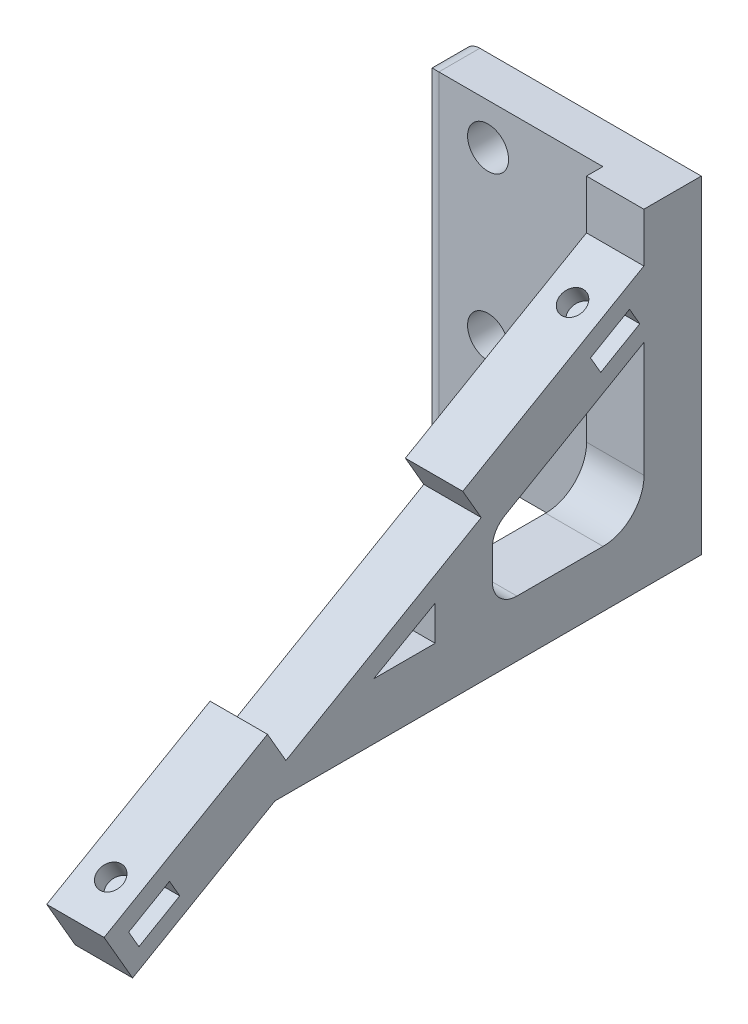
SolidWorks part; units mm, degrees
ref_plane "Front Plane" through (0, 0, 0) normal (0, 0, 1) x (1, 0, 0)
ref_plane "Top Plane" through (0, 0, 0) normal (0, 1, 0) x (1, 0, 0)
ref_plane "Right Plane" through (0, 0, 0) normal (1, 0, 0) x (0, 0, -1)
other "Mesh1"
sketch "Sketch1" plane through (0, 0, 0) normal (1, 0, 0) x (0, 0, -1)
  line L0 (-90932.5796, -4234.1019) -> (-71013.9953, 7265.8981)
  line L1 (-71013.9953, 7265.8981) -> (-68763.9953, 3368.7838)
  line L2 (-68763.9953, 3368.7838) -> (-44948.2967, 17118.7838)
  line L3 (-44948.2967, 17118.7838) -> (-47198.2967, 21015.8981)
  line L4 (-47198.2967, 21015.8981) -> (-25114.6489, 33765.8981)
  line L5 (-25114.6489, 33765.8981) -> (-25114.6489, 39765.8981)
  line L6 (-25114.6489, 39765.8981) -> (-18114.6489, 39765.8981)
  line L7 (-18114.6489, 39765.8981) -> (-18114.6489, -234.1019)
  line L8 (-90932.5796, -4234.1019) -> (-89130.3388, -4234.1019) construction
  line L9 (-18114.6489, -234.1019) -> (-70107.2704, -234.1019)
  line L10 (-70107.2704, -234.1019) -> (-87458.3031, -10251.7253)
  line L11 (-90932.5796, -4234.1019) -> (-87458.3031, -10251.7253)
  line L12 (-87940.7843, -5162.9479) -> (-82961.1382, -2287.9479)
  line L13 (-82961.1382, -2287.9479) -> (-81711.1382, -4453.0115)
  line L14 (-81711.1382, -4453.0115) -> (-86690.7843, -7328.0115)
  line L15 (-86690.7843, -7328.0115) -> (-87940.7843, -5162.9479)
  line L16 (-58064.4113, 6650.0317) -> (-50564.4113, 10900.0317)
  line L17 (-50564.4113, 10900.0317) -> (-50564.4113, 6650.0317)
  line L18 (-50564.4113, 6650.0317) -> (-58064.4113, 6650.0317)
  line L19 (-31627.1311, 27323.1447) -> (-26867.0679, 30078.4664)
  line L20 (-26867.0679, 30078.4664) -> (-25614.6489, 27914.8013)
  line L21 (-25614.6489, 27914.8013) -> (-30374.7122, 25159.4795)
  line L22 (-30374.7122, 25159.4795) -> (-31627.1311, 27323.1447)
  line L23 (-25094.8426, 25713.3197) -> (-25094.8426, 11650.0317)
  line L24 (-30094.8426, 6650.0317) -> (-40594.8426, 6650.0317)
  line L25 (-43594.8426, 13308.0426) -> (-43594.8426, 9650.0317)
  line L26 (-25094.8426, 25713.3197) -> (-42094.8426, 15873.0159)
  arc A0 (-30094.8426, 6650.0317) -> (-25094.8426, 11650.0317) centre (-30094.8426, 11650.0317) ccw
  arc A1 (-43594.8426, 9650.0317) -> (-40594.8426, 6650.0317) centre (-40594.8426, 9650.0317) ccw
  arc A2 (-42094.8426, 15873.0159) -> (-43594.8426, 13271.5835) centre (-40589.0258, 13271.5835) ccw
  dimension "D24" = 5000
  dimension "D28" = 3000
  dimension "D1" = 23000
  dimension "D2" = 4500
  dimension "D3" = 27500
  dimension "D4" = 4500
  dimension "D5" = 30
  dimension "D6" = 6000
  dimension "D7" = 25500
  dimension "D8" = 7000
  dimension "D9" = 40000
  dimension "D10" = 51992.6215
  dimension "D11" = 150
  dimension "D12" = 5500
  dimension "D13" = 2500
  dimension "D14" = 7500
  dimension "D15" = 4250
  dimension "D16" = 5750
  dimension "D17" = 2500
  dimension "D18" = 2148.2511
  dimension "D19" = 2126.5478
  dimension "D20" = 6884.1336
  dimension "D21" = 32868.1683
  dimension "D22" = 11980.1937
  dimension "D23" = 25947.4217
  dimension "D25" = 17000
  dimension "D26" = 9840.3039
  dimension "D27" = 10500
  dimension "D29" = 25393.5815
  dimension "D30" = 7500
extrude "Boss-Extrude1" add sketch "Sketch1" against normal blind 7000
ref_plane "Plane1" through (0, 36285.9881, 20949.725) normal (0, 0.866, 0.5) x (1, 0, 0)
sketch "Sketch2" plane through (0, 0, 0) normal (0, 0, 1) x (1, 0, 0)
  line L0 (-40483.4755, -7522.2196) -> (-47474.8479, -7522.2196)
sketch "Sketch3" plane through (0, 0, 0) normal (0, 0, 1) x (1, 0, 0)
  line L0 (-40477.0787, 39685.295) -> (-69477.0787, 39685.295)
  line L1 (-40477.0787, 39685.295) -> (-40477.0787, -314.705)
  line L2 (-40477.0787, -314.705) -> (-69477.0787, -314.705)
  line L3 (-69477.0787, 39685.295) -> (-69477.0787, -314.705)
  circle A0 centre (-61434.2787, 34700.8694) radius 2612.0723
  circle A1 centre (-61482.2069, 9690.1301) radius 2582.0747
  circle A2 centre (-67486.5197, 37694.736) radius 1990.559
  dimension "D1" = 29000
  dimension "D2" = 40000
  dimension "D3" = 10004.8352
  dimension "D4" = 35015.5744
  dimension "D5" = 7994.8718
sketch "Sketch6" plane through (0, 0, 0) normal (1, 0, 0) x (0, 0, -1)
  line L0 (-18114.6489, 24672.3169) -> (-23139.1932, 24672.3169)
  line L1 (-18114.6489, 39765.8981) -> (-18114.6489, -234.1019) construction
sketch "Sketch8" plane through (0, 0, 18114.6489) normal (0, 0, -1) x (-1, 0, 0)
  line L0 (29000, 39765.8981) -> (0, 39765.8981)
  line L1 (0, 39765.8981) -> (0, -234.1019)
  line L2 (0, -234.1019) -> (29000, -234.1019)
  line L3 (29000, -234.1019) -> (29000, 39765.8981)
  line L4 (21000, 14765.8981) -> (21000, 34765.8981) construction
  line L5 (7000, 39765.8981) -> (0, 39765.8981) construction
  circle A0 centre (21000, 14765.8981) radius 2500
  circle A1 centre (21000, 34765.8981) radius 2500
  dimension "D5" = 5000
  dimension "D1" = 29000
  dimension "D2" = 15000
  dimension "D3" = 35000
  dimension "D4" = 8000
extrude "Boss-Extrude3" add sketch "Sketch8" against normal blind 5000
fillet "Fillet1" radius 2000 3 edges at (-29000, -234.1019, 20614.6489) (-29000, 39765.8981, 20614.6489) (-29000, 19765.8981, 23114.6489)
sketch "Sketch9" plane through (0, 36199.3855, 20899.725) normal (0, 0.866, 0.5) x (1, 0, 0)
  line L0 (-44195.3034, -10868.8212) -> (-3500, -10868.8212) construction
  line L1 (-44228.7555, -75902.8757) -> (-3500, -75902.8757) construction
  line L2 (-40674.3613, -12602.0022) -> (-40674.3613, -7750.6514) construction
  line L3 (0, -30366.9749) -> (0, -4866.9749) construction
  line L4 (-3500, -10868.8212) -> (-3500, -75902.8757) construction
  line L5 (-7000, -4866.9749) -> (0, -4866.9749) construction
  circle A1 centre (-44228.7555, -75902.8757) radius 1517.8112 construction
  circle A2 centre (-44195.3034, -10868.8212) radius 1458.892 construction
  circle A3 centre (-3500, -10868.8212) radius 1500
  circle A4 centre (-3500, -75902.8757) radius 1500
  dimension "D1" = 2917.784
  dimension "D3" = 3000
  dimension "D4" = 3000
  dimension "D2" = 3520.9421
  dimension "D5" = 3500
extrude "Cut-Extrude1" cut sketch "Sketch9" against normal blind 7500
sketch "Sketch10" plane through (0, 36199.3855, 20899.725) normal (0, 0.866, 0.5) x (1, 0, 0)
  line L0 (-3500, -10868.8212) -> (-3500, -75902.8757) construction
  circle A2 centre (-3500, -10868.8212) radius 1500
  circle A3 centre (-3500, -75902.8757) radius 1517.9635
